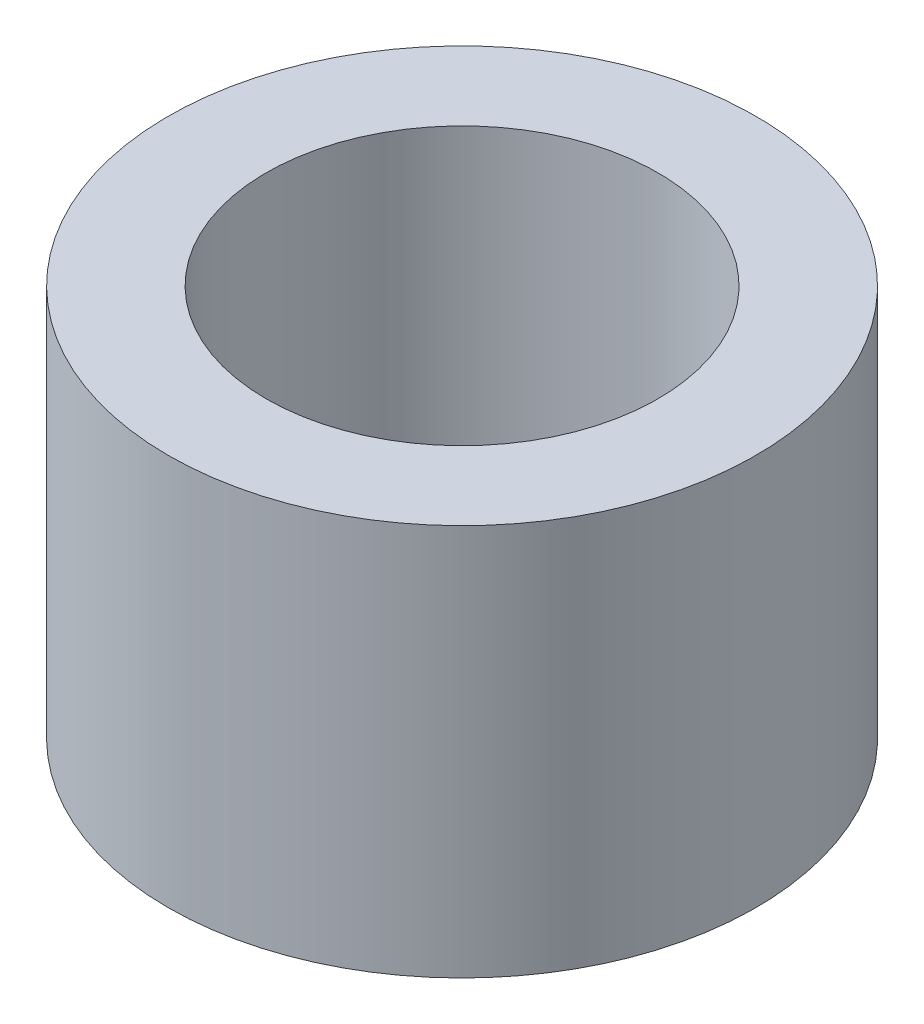
SolidWorks part; units mm, degrees
ref_plane "Ebene vorne" through (0, 0, 0) normal (0, 0, 1) x (1, 0, 0)
ref_plane "Ebene oben" through (0, 0, 0) normal (0, 1, 0) x (1, 0, 0)
ref_plane "Ebene rechts" through (0, 0, 0) normal (1, 0, 0) x (0, 0, -1)
sketch "Skizze1" plane through (0, 0, 0) normal (0, 1, 0) x (1, 0, 0)
  circle A0 centre (0, 0) radius 2
  circle A1 centre (0, 0) radius 3
  dimension "D1" = 4
  dimension "D2" = 6
extrude "Aufsatz-Linear austragen1" add sketch "Skizze1" along normal blind 4
